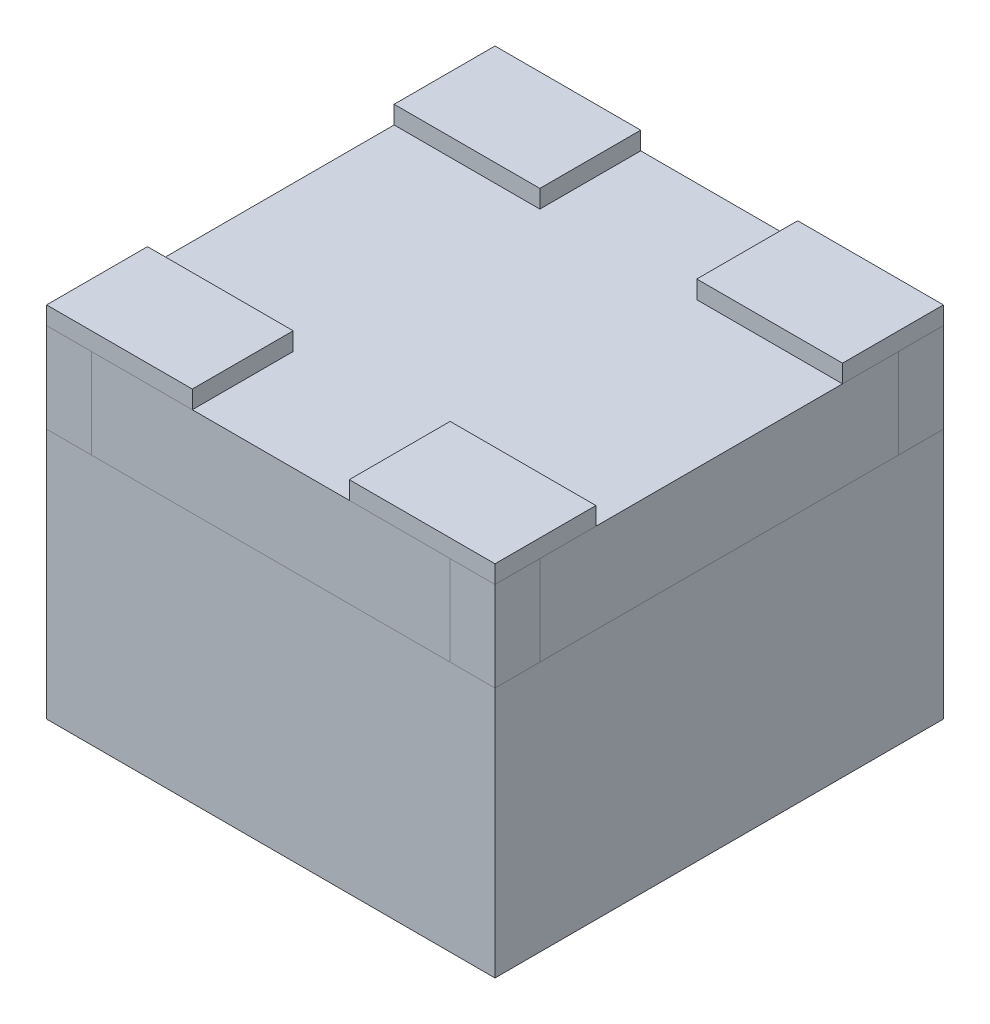
SolidWorks part; units mm, degrees
ref_plane "前视基准面" through (0, 0, 0) normal (0, 0, 1) x (1, 0, 0)
ref_plane "上视基准面" through (0, 0, 0) normal (0, 1, 0) x (1, 0, 0)
ref_plane "右视基准面" through (0, 0, 0) normal (1, 0, 0) x (0, 0, -1)
sketch "草图1" plane through (0, 0, 0) normal (0, 1, 0) x (1, 0, 0)
  line L1 (-0.9496, 0.7605) -> (0.0504, 0.7605)
  line L2 (-0.9496, 0.7605) -> (-0.9496, -0.2395)
  line L3 (-0.9496, -0.2395) -> (0.0504, -0.2395)
  line L4 (0.0504, 0.7605) -> (0.0504, -0.2395)
  line L5 (-0.9496, 0.7605) -> (0.0504, -0.2395) construction
  line L6 (-0.9496, -0.2395) -> (0.0504, 0.7605) construction
  point P0 (-0.4496, 0.2605)
  dimension "D1" = 1
  dimension "D2" = 1
extrude "凸台-拉伸1" add sketch "草图1" along normal blind 0.2
sketch "草图3" plane through (0, 0.2, 0) normal (0, 1, 0) x (1, 0, 0)
  line L0 (-0.9496, 0.7605) -> (-0.6246, 0.7605)
  line L1 (-0.9496, 0.7605) -> (-0.9496, 0.5355)
  line L2 (-0.6246, 0.7605) -> (-0.6246, 0.5355)
  line L3 (-0.9496, 0.5355) -> (-0.6246, 0.5355)
  line L4 (0.0504, 0.7605) -> (-0.9496, 0.7605) construction
  line L9 (0.0504, 0.7605) -> (0.0504, 0.5355)
  line L10 (0.0504, 0.7605) -> (-0.2746, 0.7605)
  line L11 (0.0504, 0.5355) -> (-0.2746, 0.5355)
  line L12 (-0.2746, 0.7605) -> (-0.2746, 0.5355)
  line L13 (0.0504, -0.2395) -> (0.0504, 0.7605) construction
  line L14 (-0.9496, -0.2395) -> (-0.6246, -0.2395)
  line L15 (-0.9496, -0.2395) -> (-0.9496, -0.0145)
  line L16 (-0.6246, -0.2395) -> (-0.6246, -0.0145)
  line L17 (-0.9496, -0.0145) -> (-0.6246, -0.0145)
  line L18 (-0.9496, -0.2395) -> (0.0504, -0.2395) construction
  line L19 (0.0504, -0.2395) -> (0.0504, -0.0145)
  line L20 (0.0504, -0.2395) -> (-0.2746, -0.2395)
  line L21 (0.0504, -0.0145) -> (-0.2746, -0.0145)
  line L22 (-0.2746, -0.2395) -> (-0.2746, -0.0145)
  dimension "D1" = 0.325
  dimension "D2" = 0.225
extrude "凸台-拉伸2" add sketch "草图3" along normal blind 0.04 separate body
sketch "草图4" plane through (0, 0, 0) normal (0, -1, 0) x (1, 0, 0)
  line L0 (-0.9496, 0.2395) -> (-0.5496, 0.2395)
  line L1 (-0.9496, 0.2395) -> (-0.9496, -0.7605)
  line L2 (-0.5496, 0.2395) -> (-0.5496, -0.7605)
  line L3 (-0.9496, -0.7605) -> (-0.5496, -0.7605)
  line L4 (-0.9496, 0.2395) -> (0.0504, 0.2395) construction
  line L17 (-0.9496, -0.7605) -> (-0.9496, 0.2395) construction
  line L18 (-0.2746, 0.2395) -> (0.0504, 0.2395)
  line L19 (-0.2746, 0.2395) -> (-0.2746, -0.7605)
  line L20 (-0.2746, -0.7605) -> (0.0504, -0.7605)
  line L21 (0.0504, 0.2395) -> (0.0504, -0.7605)
  point P10 (0, 0)
  point P14 (0, 0)
  dimension "D1" = 0.325
  dimension "D2" = 0.4
  dimension "D3" = 1
extrude "凸台-拉伸3" add sketch "草图4" along normal blind 0.04 separate body
sketch "草图5" plane through (0, -0.04, 0) normal (0, -1, 0) x (1, 0, 0)
  line L0 (-0.9496, 0.2395) -> (-0.9496, -0.7605) construction
  line L1 (-0.9246, -0.0605) -> (-0.5746, -0.0605)
  line L2 (-0.9246, -0.0605) -> (-0.9246, -0.4605)
  line L3 (-0.9246, -0.4605) -> (-0.5746, -0.4605)
  line L4 (-0.5746, -0.0605) -> (-0.5746, -0.4605)
  line L5 (-0.5496, 0.2395) -> (-0.9496, 0.2395) construction
  dimension "D1" = 0.4
  dimension "D2" = 0.35
  dimension "D3" = 0.025
  dimension "D4" = 0.3
extrude "凸台-拉伸4" add sketch "草图5" along normal blind 0.05 separate body
sketch "草图7" plane through (0, -0.04, 0) normal (0, -1, 0) x (1, 0, 0)
  line L0 (0.0504, 0.2395) -> (-0.2746, 0.2395) construction
  line L1 (-0.1646, -0.0105) -> (-0.0646, -0.0105)
  line L2 (-0.1646, -0.0105) -> (-0.1646, -0.1105)
  line L3 (-0.1646, -0.1105) -> (-0.0646, -0.1105)
  line L4 (-0.0646, -0.0105) -> (-0.0646, -0.1105)
  line L5 (-0.1646, -0.4105) -> (-0.0646, -0.4105)
  line L6 (-0.1646, -0.4105) -> (-0.1646, -0.5105)
  line L7 (-0.1646, -0.5105) -> (-0.0646, -0.5105)
  line L8 (-0.0646, -0.4105) -> (-0.0646, -0.5105)
  line L9 (-0.1646, -0.1605) -> (-0.0646, -0.1605)
  line L10 (-0.1646, -0.1605) -> (-0.1646, -0.3605)
  line L11 (-0.1646, -0.3605) -> (-0.0646, -0.3605)
  line L12 (-0.0646, -0.1605) -> (-0.0646, -0.3605)
  line L13 (0.0504, -0.7605) -> (0.0504, 0.2395) construction
  dimension "D1" = 0.1
  dimension "D2" = 0.2
  dimension "D3" = 0.05
  dimension "D4" = 0.05
  dimension "D5" = 0.25
  dimension "D6" = 0.115
extrude "凸台-拉伸5" add sketch "草图7" along normal blind 0.05 separate body
sketch "草图8" plane through (0, 0, 0) normal (0, -1, 0) x (1, 0, 0)
  line L4 (0.0504, -0.7605) -> (0.0504, 0.2395)
  line L5 (0.0504, 0.2395) -> (-0.9496, 0.2395)
  line L6 (-0.9496, 0.2395) -> (-0.9496, -0.7605)
  line L7 (-0.9496, -0.7605) -> (0.0504, -0.7605)
  line L8 (0.0504, -0.7605) -> (0.0504, 0.2395)
  line L9 (0.0504, 0.2395) -> (-0.9496, 0.2395)
  line L10 (-0.9496, 0.2395) -> (-0.9496, -0.7605)
  line L11 (-0.9496, -0.7605) -> (0.0504, -0.7605)
  dimension "D1" = 0
extrude "凸台-拉伸6" add sketch "草图8" along normal blind 0.56 separate body
sketch "草图11" plane through (-0.9496, 0, 0) normal (-1, 0, 0) x (0, 0, 1)
  line L0 (-0.7605, 0.2) -> (-0.6605, 0.2)
  line L1 (-0.7605, 0.2) -> (-0.7605, 0)
  line L2 (-0.6605, 0.2) -> (-0.6605, 0)
  line L3 (-0.7605, 0) -> (-0.6605, 0)
  line L4 (-0.7605, 0.2) -> (0.2395, 0.2) construction
  line L6 (-0.7605, 0) -> (0.2395, 0) construction
  dimension "D1" = 0.1
sketch "草图12" plane through (-0.9496, 0, 0) normal (-1, 0, 0) x (0, 0, 1)
  line L0 (0.2395, 0.2) -> (0.1395, 0.2)
  line L1 (0.2395, 0.2) -> (0.2395, 0)
  line L2 (0.1395, 0.2) -> (0.1395, 0)
  line L3 (0.2395, 0) -> (0.1395, 0)
  line L4 (0.0145, 0.2) -> (0.2395, 0.2) construction
  line L5 (-0.7605, 0.2) -> (-0.6605, 0.2) construction
  line L6 (-0.7605, 0) -> (0.2395, 0) construction
  line L7 (-0.6605, 0.2) -> (-0.6605, 0) construction
extrude "切除-拉伸1" cut sketch "草图12" against normal blind 0.1
extrude "切除-拉伸2" cut sketch "草图11" against normal blind 0.1
sketch "草图16" plane through (0.0504, 0, 0) normal (1, 0, 0) x (0, 0, -1)
  line L0 (-0.2395, 0.2) -> (-0.1395, 0.2)
  line L1 (-0.2395, 0.2) -> (-0.2395, 0)
  line L2 (-0.1395, 0.2) -> (-0.1395, 0)
  line L3 (-0.2395, 0) -> (-0.1395, 0)
  line L4 (-0.2395, 0.2) -> (-0.0145, 0.2) construction
  line L6 (-0.2395, 0) -> (0.7605, 0) construction
  line L7 (0.7605, 0.2) -> (0.6605, 0.2)
  line L8 (0.7605, 0.2) -> (0.7605, 0)
  line L9 (0.6605, 0.2) -> (0.6605, 0)
  line L10 (0.7605, 0) -> (0.6605, 0)
  line L11 (0.5355, 0.2) -> (0.7605, 0.2) construction
  dimension "D1" = 0.1
extrude "切除-拉伸3" cut sketch "草图16" against normal blind 0.1
sketch "草图18" plane through (-0.0496, 0, 0) normal (1, 0, 0) x (0, 0, -1)
  line L4 (-0.2395, 0.2) -> (-0.2395, 0)
  line L5 (-0.2395, 0) -> (-0.1395, 0)
  line L6 (-0.1395, 0) -> (-0.1395, 0.2)
  line L7 (-0.1395, 0.2) -> (-0.2395, 0.2)
  line L8 (-0.2395, 0.2) -> (-0.2395, 0)
  line L9 (-0.2395, 0) -> (-0.1395, 0)
  line L10 (-0.1395, 0) -> (-0.1395, 0.2)
  line L11 (-0.1395, 0.2) -> (-0.2395, 0.2)
  dimension "D1" = 0
extrude "凸台-拉伸7" add sketch "草图18" along normal blind 0.1 separate body
sketch "草图19" plane through (-0.0496, 0, 0) normal (1, 0, 0) x (0, 0, -1)
  line L4 (0.7605, 0) -> (0.7605, 0.2)
  line L5 (0.7605, 0.2) -> (0.6605, 0.2)
  line L6 (0.6605, 0.2) -> (0.6605, 0)
  line L7 (0.6605, 0) -> (0.7605, 0)
  line L8 (0.7605, 0) -> (0.7605, 0.2)
  line L9 (0.7605, 0.2) -> (0.6605, 0.2)
  line L10 (0.6605, 0.2) -> (0.6605, 0)
  line L11 (0.6605, 0) -> (0.7605, 0)
  dimension "D1" = 0
extrude "凸台-拉伸8" add sketch "草图19" along normal blind 0.1 separate body
sketch "草图20" plane through (-0.8496, 0, 0) normal (-1, 0, 0) x (0, 0, 1)
  line L4 (0.2395, 0) -> (0.2395, 0.2)
  line L5 (0.2395, 0.2) -> (0.1395, 0.2)
  line L6 (0.1395, 0.2) -> (0.1395, 0)
  line L7 (0.1395, 0) -> (0.2395, 0)
  line L8 (0.2395, 0) -> (0.2395, 0.2)
  line L9 (0.2395, 0.2) -> (0.1395, 0.2)
  line L10 (0.1395, 0.2) -> (0.1395, 0)
  line L11 (0.1395, 0) -> (0.2395, 0)
  dimension "D1" = 0
extrude "凸台-拉伸9" add sketch "草图20" along normal blind 0.1 separate body
sketch "草图21" plane through (-0.8496, 0, 0) normal (-1, 0, 0) x (0, 0, 1)
  line L4 (-0.7605, 0.2) -> (-0.7605, 0)
  line L5 (-0.7605, 0) -> (-0.6605, 0)
  line L6 (-0.6605, 0) -> (-0.6605, 0.2)
  line L7 (-0.6605, 0.2) -> (-0.7605, 0.2)
  line L8 (-0.7605, 0.2) -> (-0.7605, 0)
  line L9 (-0.7605, 0) -> (-0.6605, 0)
  line L10 (-0.6605, 0) -> (-0.6605, 0.2)
  line L11 (-0.6605, 0.2) -> (-0.7605, 0.2)
  dimension "D1" = 0
extrude "凸台-拉伸10" add sketch "草图21" along normal blind 0.1 separate body
